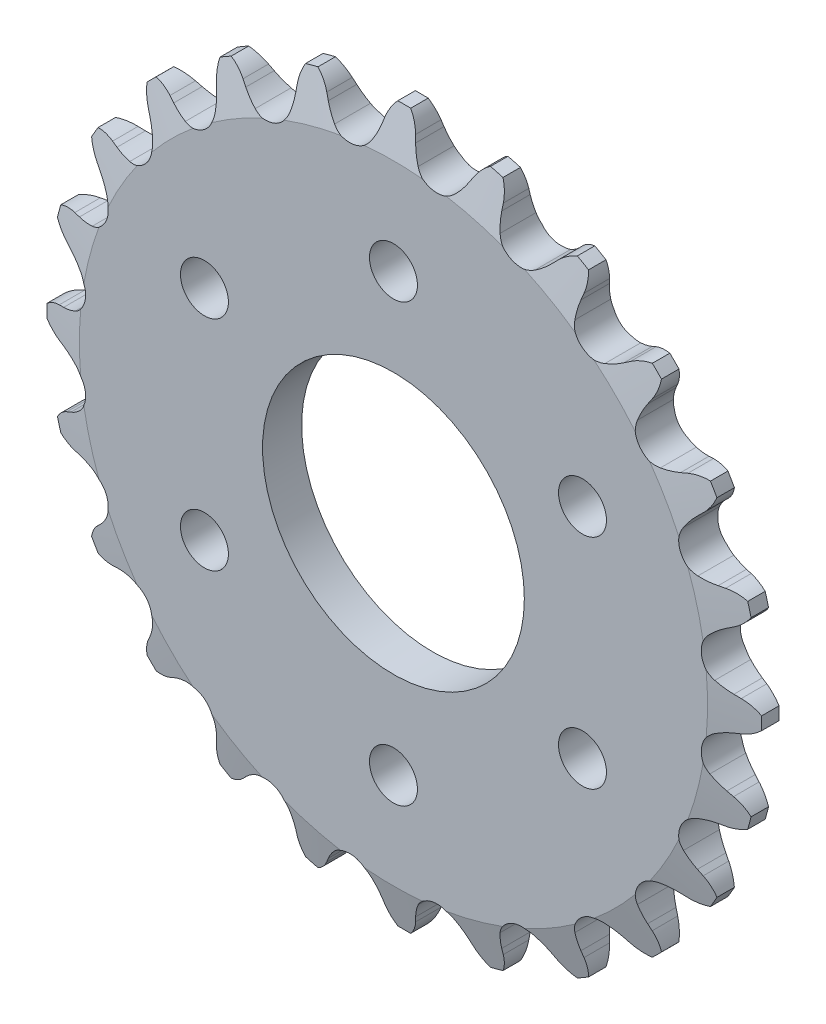
SolidWorks part; units mm, degrees
ref_plane "Front Plane" through (0, 0, 0) normal (0, 0, 1) x (1, 0, 0)
ref_plane "Top Plane" through (0, 0, 0) normal (0, 1, 0) x (1, 0, 0)
ref_plane "Right Plane" through (0, 0, 0) normal (1, 0, 0) x (0, 0, -1)
sketch "Sketch0" plane through (0, 0, 0) normal (0, 0, 1) x (1, 0, 0)
  line L0 (4.7625, -36.1748) -> (0, 0) construction
  line L1 (0, 0) -> (13.9629, -33.7095) construction
  line L2 (0, 0) -> (-4.7625, -36.1748) construction
  line L3 (4.7625, -36.1748) -> (13.9629, -33.7095) construction
  line L4 (4.7625, -36.1748) -> (-4.7625, -36.1748) construction
  line L5 (8.0153, -36.3665) -> (7.6904, -35.7883)
  line L6 (4.7625, -36.1748) -> (0, -36.8018) construction
  line L7 (1.6702, -37.2019) -> (1.8344, -36.5593)
  line L8 (0, -36.1748) -> (0, -39.0323) construction
  line L9 (6.5945, -34.3428) -> (1.8888, -39.0485) construction
  line L10 (0, 0) -> (0, -36.1748) construction
  line L11 (7.6904, -35.7883) -> (1.8888, -39.0485) construction
  line L12 (0, -39.0323) -> (0, -39.5942) construction
  line L13 (11.6322, -34.3341) -> (8.0153, -36.3665) construction
  circle A0 centre (0, 0) radius 39.0323 construction
  circle A1 centre (0, 0) radius 36.4869 construction
  arc A2 (-2.6184, -40.3149) -> (12.9634, -38.2635) centre (0, 0) ccw
  circle A3 centre (0, 0) radius 39.5942 construction
  circle A4 centre (4.7625, -36.1748) radius 2.54 construction
  arc A7 (6.5945, -34.3428) -> (2.5188, -34.8794) centre (4.7625, -36.1748) ccw
  circle A8 centre (4.7625, -36.1748) radius 2.5908 construction
  arc A9 (8.0153, -36.3665) -> (12.9634, -38.2635) centre (11.6322, -34.3341) ccw
  arc A10 (7.6904, -35.7883) -> (6.5945, -34.3428) centre (1.8888, -39.0485) ccw
  arc A11 (1.6702, -37.2019) -> (-2.6184, -40.3149) centre (-2.3495, -36.1748) cw
  arc A12 (1.8344, -36.5593) -> (2.5188, -34.8794) centre (8.282, -38.2068) cw
  dimension "D1" = 2.5908
  dimension "Dr" = 5.08
  dimension "Ds" = 5.1816
  dimension "R" = 2.5908
  dimension "Pitch" = 9.525
  dimension "A" = 37.5
  dimension "360/N" = 15
  dimension "B" = 15.667
  dimension "ab" = 7.112
  dimension "J" = 2.8575
  dimension "ac" = 4.064
sketch "Sketch1" plane through (0, 0, 0) normal (1, 0, 0) x (0, 0, -1)
  line L0 (2.1336, 0) -> (-2.1336, 0)
  line L1 (-2.1336, 0) -> (-2.1336, 34.2698)
  line L2 (-2.1336, 34.2698) -> (-0.943, 39.0323)
  line L3 (-0.943, 39.0323) -> (0.943, 39.0323)
  line L4 (0.943, 39.0323) -> (2.1336, 34.2698)
  line L5 (2.1336, 34.2698) -> (2.1336, 0)
  line L7 (0, 39.0323) -> (0, 0) construction
  line L8 (-2.1336, 34.2698) -> (2.1336, 34.2698) construction
  line L9 (0, 39.0323) -> (0, -39.0323) construction
  line L10 (-2.1336, 34.2698) -> (-2.1336, 39.0323) construction
  line L11 (-2.1336, 39.0323) -> (-0.943, 39.0323) construction
  line L12 (0.943, 39.0323) -> (2.1336, 39.0323) construction
  line L13 (2.1336, 39.0323) -> (2.1336, 34.2698) construction
  dimension "t" = 4.2672
  dimension "g" = 1.1906
  dimension "h" = 4.7625
revolve "Revolve1" add sketch "Sketch1" angle 360 mid plane about L0
extrude "Cut-Extrude1" cut sketch "Sketch0" against normal through all and the other way through all
pattern_circular "CirPattern1" count 24 over 360 about axis through (0, 0, 0) along (0, 0, 1) of "Cut-Extrude1"
sketch "Sketch2" plane through (0, 0, 0) normal (0, 0, 1) x (1, 0, 0)
  circle A0 centre (0, 0) radius 14.2812 construction
  circle A1 centre (0, 0) radius 30.1625
  circle A2 centre (0, 0) radius 38.989 construction
  dimension "Bore" = 28.5623
  dimension "Hub Dia." = 60.325
  dimension "OD" = 77.978
sketch "Sketch3" plane through (0, 0, 0) normal (0, 0, 1) x (1, 0, 0)
  circle A0 centre (0, 0) radius 14.2812 construction
  circle A1 centre (0, 0) radius 14.2812
  circle A2 centre (0, 0) radius 38.989 construction
  circle A3 centre (0, 0) radius 38.989
extrude "Cut-Extrude2" cut sketch "Sketch3" along normal through all and the other way through all flip side to cut
sketch "Sketch4" plane through (0, 0, 2.1336) normal (0, 0, 1) x (1, 0, 0)
  circle A0 centre (0, 23.8125) radius 2.6162
  circle A1 centre (20.6222, 11.9063) radius 2.6162
  circle A2 centre (20.6222, -11.9062) radius 2.6162
  circle A3 centre (0, -23.8125) radius 2.6162
  circle A4 centre (-20.6222, -11.9063) radius 2.6162
  circle A5 centre (-20.6222, 11.9062) radius 2.6162
  point P2 (-24.7648, 12.2709)
  point P3 (0, 0)
  point P14 (0, 0)
  point P16 (0, 0)
  dimension "D3" = 5.2324
  dimension "D2" = 47.625
  dimension "D1" = 6
extrude "Cut-Extrude3" cut sketch "Sketch4" against normal through all
equation "\"360/N@Sketch0\" = 360/\"Teeth@CirPattern1\""
equation "\"Ds@Sketch0\" = 1.005 * \"Dr@Sketch0\" + 0.003"
equation "\"R@Sketch0\" = 1/2 * \"Ds@Sketch0\""
equation "\"A@Sketch0\" = 35 +  ( 60 / \"Teeth@CirPattern1\" ) "
equation "\"B@Sketch0\" = 18 -  ( 56 / \"Teeth@CirPattern1\" )"
equation "\"ac@Sketch0\" = 0.8 * \"Dr@Sketch0\""
equation "\"ab@Sketch0\" = 1.4 * \"Dr@Sketch0\""
equation "\"J@Sketch0\" = 0.3 * \"Pitch@Sketch0\""
equation "\"h@Sketch1\" = \"Pitch@Sketch0\" / 2"
equation "\"g@Sketch1\" = \"h@Sketch1\" / 4"
